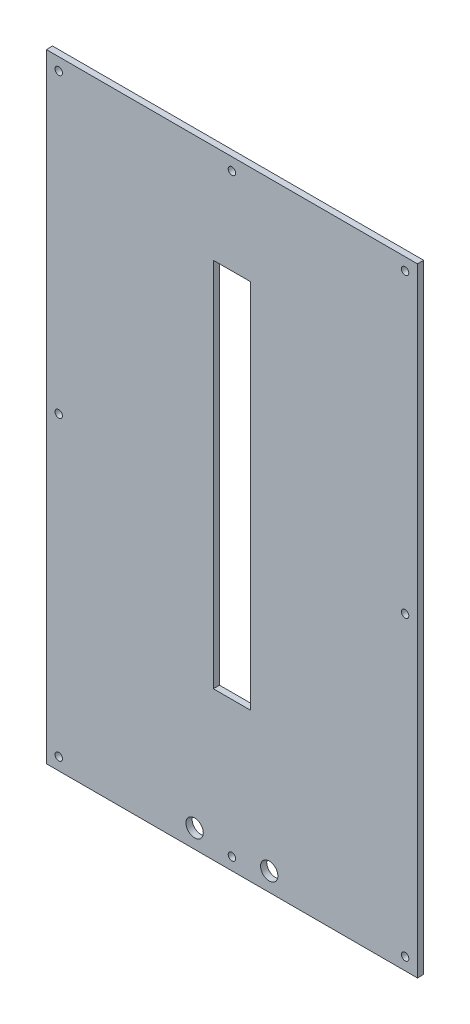
SolidWorks part; units mm, degrees
material "ABS"
ref_plane "Front Plane" through (0, 0, 0) normal (0, 0, 1) x (1, 0, 0)
ref_plane "Top Plane" through (0, 0, 0) normal (0, 1, 0) x (1, 0, 0)
ref_plane "Right Plane" through (0, 0, 0) normal (1, 0, 0) x (0, 0, -1)
sketch "Sketch1" plane through (0, 0, 0) normal (0, 0, 1) x (1, 0, 0)
  line L0 (0, 175) -> (0, -325) construction
  line L1 (-150, -325) -> (150, -325)
  line L2 (-150, -325) -> (-150, 175)
  line L3 (-150, 175) -> (150, 175)
  line L4 (150, -325) -> (150, 175)
  line L5 (-30.15, -310) -> (30.15, -310) construction
  line L7 (-140, 175) -> (-140, -325) construction
  line L9 (-15, 95) -> (15, 95)
  line L10 (-15, 95) -> (-15, -205)
  line L11 (-15, -205) -> (15, -205)
  line L12 (15, 95) -> (15, -205)
  circle A2 centre (-140, -75) radius 3
  circle A3 centre (140, -315) radius 3
  circle A4 centre (140, -75) radius 3
  circle A5 centre (140, 165) radius 3
  circle A6 centre (0, 165) radius 3
  circle A7 centre (0, -315) radius 3
  circle A8 centre (-140, 165) radius 3
  circle A9 centre (-140, -315) radius 3
  circle A10 centre (-30.15, -310) radius 7
  circle A11 centre (30.15, -310) radius 7
  point P0 (0, 0)
  point P27 (0, 0)
  point P35 (0, -310)
  dimension "D4" = 6
  dimension "D6" = 10
  dimension "D8" = 6
  dimension "D17" = 14
  dimension "D1" = 300
  dimension "D2" = 500
  dimension "D3" = 10
  dimension "D5" = 10
  dimension "D7" = 10
  dimension "D9" = 10
  dimension "D10" = 10
  dimension "D11" = 10
  dimension "D12" = 10
  dimension "D13" = 10
  dimension "D14" = 300
  dimension "D15" = 30
  dimension "D16" = 120
  dimension "D18" = 60.3
  dimension "D19" = 15
  dimension "D20" = 10
extrude "Boss-Extrude1" add sketch "Sketch1" along normal blind 5
